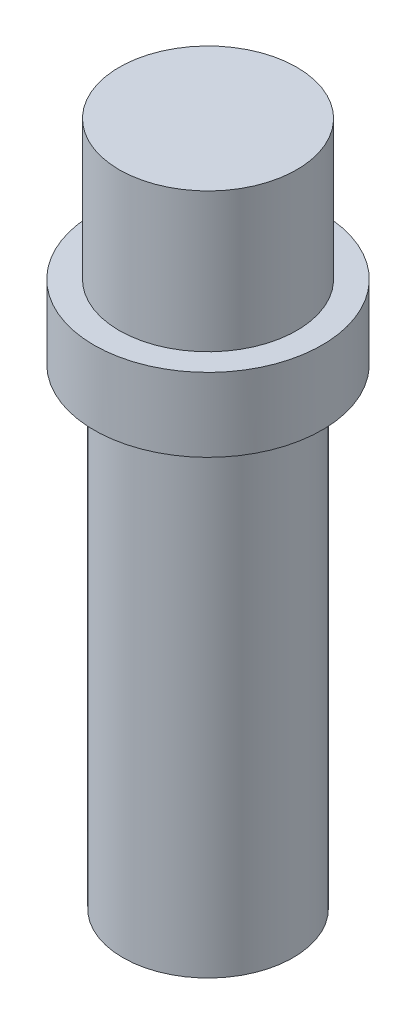
SolidWorks part; units mm, degrees
ref_plane "Front Plane" through (0, 0, 0) normal (0, 0, 1) x (1, 0, 0)
ref_plane "Top Plane" through (0, 0, 0) normal (0, 1, 0) x (1, 0, 0)
ref_plane "Right Plane" through (0, 0, 0) normal (1, 0, 0) x (0, 0, -1)
sketch "Sketch1" plane through (0, 0, 0) normal (0, 1, 0) x (1, 0, 0)
  circle A0 centre (0, 0) radius 1.4
  dimension "D1" = 2.8
extrude "Boss-Extrude1" add sketch "Sketch1" along normal blind 11.25
sketch "Sketch2" plane through (0, 11.25, 0) normal (0, 1, 0) x (1, 0, 0)
  circle A0 centre (0, 0) radius 1.46
  dimension "D1" = 2.92
extrude "Boss-Extrude2" add sketch "Sketch2" against normal blind 3.5
sketch "Sketch3" plane through (0, 7.75, 0) normal (0, -1, 0) x (1, 0, 0)
  circle A0 centre (0, 0) radius 1.875
  dimension "D1" = 3.75
extrude "Boss-Extrude3" add sketch "Sketch3" against normal offset from surface (1.21 mm away) 2.29 up to face at (0, 11.25, 1.46)
